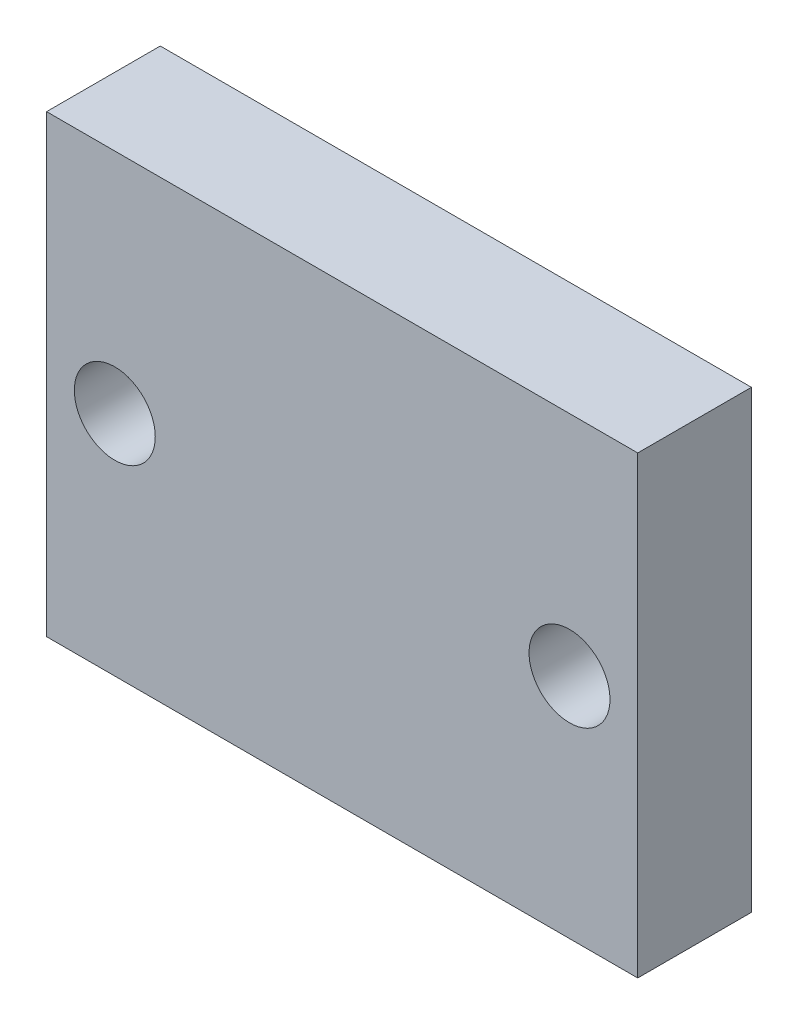
SolidWorks part; units mm, degrees
ref_plane "Front Plane" through (0, 0, 0) normal (0, 0, 1) x (1, 0, 0)
ref_plane "Top Plane" through (0, 0, 0) normal (0, 1, 0) x (1, 0, 0)
ref_plane "Right Plane" through (0, 0, 0) normal (1, 0, 0) x (0, 0, -1)
sketch "Sketch2" plane through (0, 0, 0) normal (0, 0, 1) x (1, 0, 0)
  line L1 (0, 0) -> (16.51, 0)
  line L2 (0, 0) -> (0, 12.7)
  line L3 (0, 12.7) -> (16.51, 12.7)
  line L4 (16.51, 0) -> (16.51, 12.7)
  line L5 (0, 0) -> (16.51, 12.7) construction
  line L6 (0, 12.7) -> (16.51, 0) construction
  point P4 (8.255, 6.35)
  dimension "D1" = 16.51
  dimension "D2" = 12.7
extrude "Boss-Extrude1" add sketch "Sketch2" along normal blind 3.175
sketch "Sketch3" plane through (0, 0, 3.175) normal (0, 0, 1) x (1, 0, 0)
  line L0 (0, 0) -> (16.51, 0) construction
  line L1 (0, 6.35) -> (1.905, 6.35) construction
  line L8 (0, 12.7) -> (0, 0) construction
  line L10 (16.51, 6.35) -> (14.605, 6.35) construction
  line L11 (16.51, 0) -> (16.51, 12.7) construction
  circle A0 centre (1.905, 6.35) radius 1.1303
  circle A1 centre (14.605, 6.35) radius 1.1303
  dimension "D1" = 2.2606
  dimension "D2" = 6.35
  dimension "D3" = 12.7
extrude "Cut-Extrude1" cut sketch "Sketch3" against normal through all
